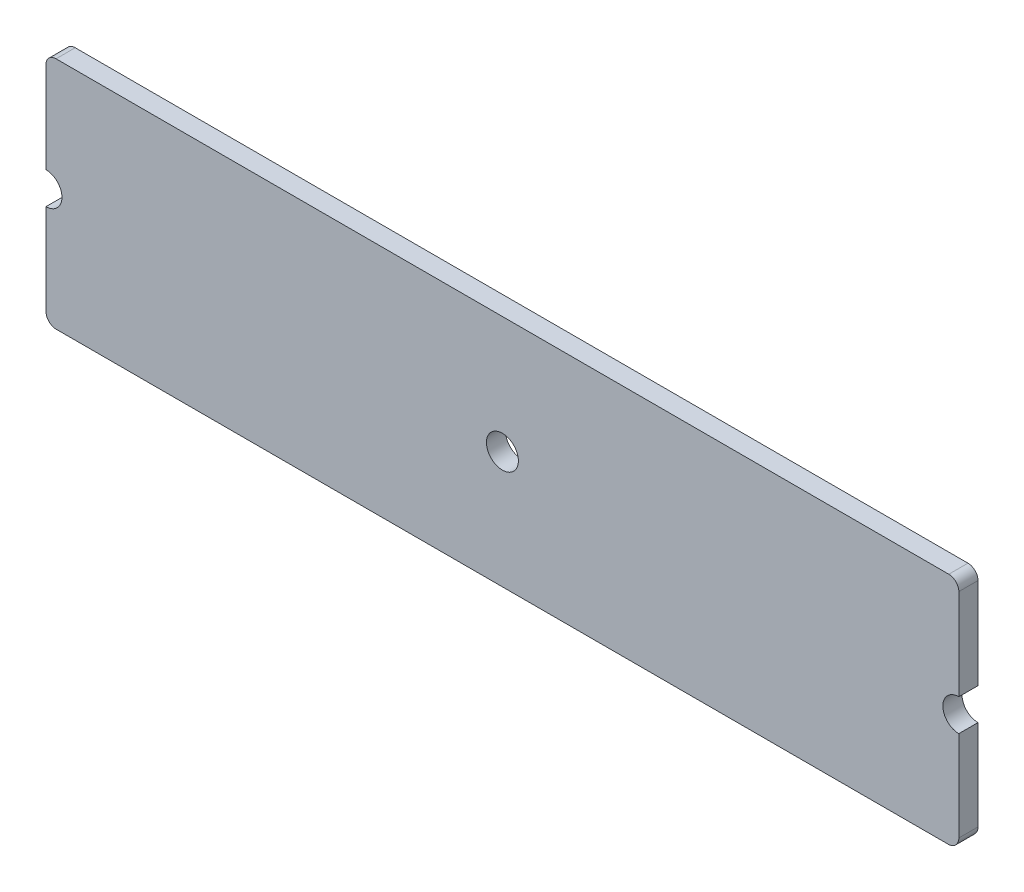
SolidWorks part; units mm, degrees
ref_plane "Спереди" through (0, 0, 0) normal (0, 0, 1) x (1, 0, 0)
ref_plane "Сверху" through (0, 0, 0) normal (0, 1, 0) x (1, 0, 0)
ref_plane "Справа" through (0, 0, 0) normal (1, 0, 0) x (0, 0, -1)
ref_plane "Плоскость1" through (0, 0, 0) normal (0, 0, -1) x (-1, 0, 0)
sketch "Эскиз1" plane through (0, 0, 0) normal (0, 0, -1) x (-1, 0, 0)
  line L0 (-10, 52.3) -> (-10, 60.9499)
  line L1 (-10, 67.0501) -> (-10, 75.725)
  line L2 (-11.1, 76.825) -> (-108.9, 76.825)
  line L3 (-110, 75.725) -> (-110, 67.0499)
  line L4 (-110, 60.9501) -> (-110, 52.35)
  line L5 (-108.825, 51.175) -> (-11.125, 51.175)
  line L6 (-110, 67.0499) -> (-110, 65.75)
  line L7 (-110, 60.9501) -> (-110, 62.25)
  line L9 (-10, 67.0501) -> (-10, 65.75)
  line L10 (-10, 62.25) -> (-10, 60.9499)
  arc A0 (-11.125, 51.175) -> (-10, 52.3) centre (-11.125, 52.3) ccw
  arc A2 (-10, 75.725) -> (-11.1, 76.825) centre (-11.0994, 75.7256) ccw
  arc A3 (-108.9, 76.825) -> (-110, 75.725) centre (-108.9006, 75.7256) ccw
  arc A4 (-10, 65.75) -> (-10, 62.25) centre (-10, 64) ccw
  arc A5 (-110, 52.35) -> (-108.825, 51.175) centre (-108.8255, 52.3495) ccw
  circle A6 centre (-60, 64) radius 1.75
  arc A7 (-110, 62.25) -> (-110, 65.75) centre (-110, 64) ccw
extrude "Бобышка-Вытянуть1" add sketch "Эскиз1" against normal blind 2.1
